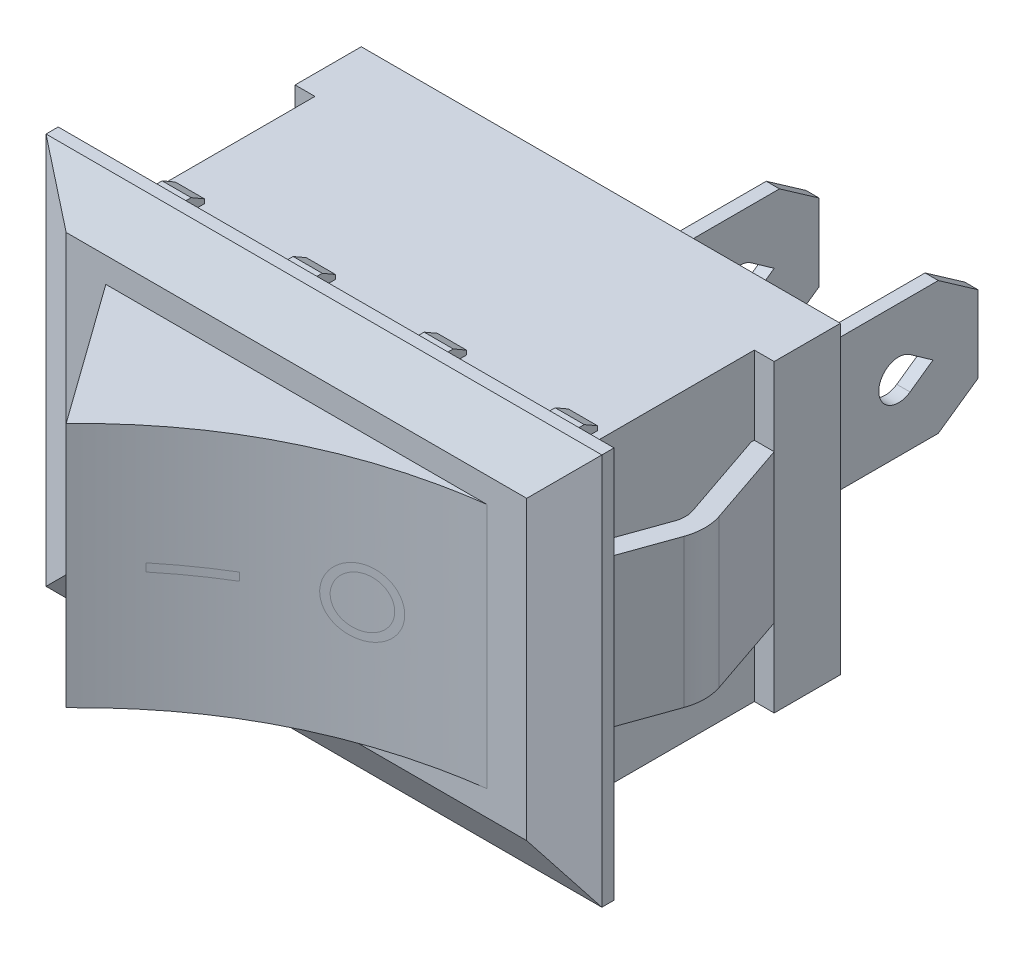
SolidWorks part; units mm, degrees
ref_plane "Front Plane" through (0, 0, 0) normal (0, 0, 1) x (1, 0, 0)
ref_plane "Top Plane" through (0, 0, 0) normal (0, 1, 0) x (1, 0, 0)
ref_plane "Right Plane" through (0, 0, 0) normal (1, 0, 0) x (0, 0, -1)
sketch "Sketch1" plane through (0, 0, 0) normal (0, 0, 1) x (1, 0, 0)
  line L1 (-8.3, -5.75) -> (8.3, -5.75)
  line L2 (-8.3, -5.75) -> (-8.3, 5.75)
  line L3 (-8.3, 5.75) -> (8.3, 5.75)
  line L4 (8.3, -5.75) -> (8.3, 5.75)
  line L5 (-8.3, -5.75) -> (8.3, 5.75) construction
  line L6 (-8.3, 5.75) -> (8.3, -5.75) construction
  point P0 (0, 0)
  dimension "D1" = 16.6
  dimension "D2" = 11.5
extrude "Boss-Extrude1" add sketch "Sketch1" along normal blind 10
sketch "Sketch2" plane through (0, 0, 10) normal (0, 0, 1) x (1, 0, 0)
  line L1 (-10.5, -7.4) -> (10.5, -7.4)
  line L2 (-10.5, -7.4) -> (-10.5, 7.4)
  line L3 (-10.5, 7.4) -> (10.5, 7.4)
  line L4 (10.5, -7.4) -> (10.5, 7.4)
  line L5 (-10.5, -7.4) -> (10.5, 7.4) construction
  line L6 (-10.5, 7.4) -> (10.5, -7.4) construction
  point P0 (0, 0)
  dimension "D1" = 14.8
  dimension "D2" = 21
extrude "Boss-Extrude2" add sketch "Sketch2" along normal blind 1.5
sketch "Sketch3" plane through (0, 0, 0) normal (0, 0, -1) x (-1, 0, 0)
  line L1 (-6.25, -2.5) -> (-5.75, -2.5)
  line L2 (-6.25, -2.5) -> (-6.25, 2.5)
  line L3 (-6.25, 2.5) -> (-5.75, 2.5)
  line L4 (-5.75, -2.5) -> (-5.75, 2.5)
  line L5 (-6.25, -2.5) -> (-5.75, 2.5) construction
  line L6 (-6.25, 2.5) -> (-5.75, -2.5) construction
  line L7 (-0.25, -2.5) -> (0.25, -2.5)
  line L8 (-0.25, -2.5) -> (-0.25, 2.5)
  line L9 (-0.25, 2.5) -> (0.25, 2.5)
  line L10 (0.25, -2.5) -> (0.25, 2.5)
  line L11 (-0.25, -2.5) -> (0.25, 2.5) construction
  line L12 (-0.25, 2.5) -> (0.25, -2.5) construction
  point P0 (-6, 0)
  point P5 (0, 0)
  dimension "D1" = 0.5
  dimension "D2" = 5
  dimension "D3" = 5
  dimension "D4" = 6
  dimension "D5" = 0.5
extrude "Boss-Extrude3" add sketch "Sketch3" along normal blind 8
sketch "Sketch4" plane through (6.25, 0, 0) normal (1, 0, 0) x (0, 0, -1)
  line L0 (2, 2.5) -> (2, 2.1)
  line L1 (8, 2.5) -> (0, 2.5) construction
  line L2 (2, 2.1) -> (2.5, 2.1)
  line L3 (2.5, 2.1) -> (2.5, 2.5)
  line L4 (0, 0) -> (8, 0) construction
  line L5 (8, 2.5) -> (8, -2.5) construction
  line L6 (0, 0.75) -> (0, -0.75)
  line L7 (2, 2.5) -> (2.5, 2.5)
  line L8 (6.5, 2.5) -> (8, 1.4497)
  line L9 (6.5, 2.5) -> (8, 2.5)
  line L10 (8, 2.5) -> (8, 1.4497)
  line L11 (5.4327, 0.6126) -> (6.3, 0)
  line L12 (5.4327, -0.6126) -> (6.3, 0)
  line L13 (8, -2.5) -> (8, -1.4497)
  line L14 (6.5, -2.5) -> (8, -2.5)
  line L15 (6.5, -2.5) -> (8, -1.4497)
  line L16 (2, -2.1) -> (2.5, -2.1)
  line L17 (2, -2.5) -> (2, -2.1)
  line L18 (2, -2.5) -> (2.5, -2.5)
  line L19 (2.5, -2.1) -> (2.5, -2.5)
  arc A0 (0, -0.75) -> (0, 0.75) centre (0, 0) ccw
  arc A1 (5.4327, 0.6126) -> (5.4327, -0.6126) centre (5, 0) ccw
  dimension "D1" = 1.5
  dimension "D7" = 1.5
  dimension "D2" = 0.5
  dimension "D3" = 0.4
  dimension "D4" = 2
  dimension "D5" = 35
  dimension "D6" = 1.5
  dimension "D8" = 5
  dimension "D9" = 1.3
extrude "Cut-Extrude1" cut sketch "Sketch4" against normal through all
sketch "Sketch5" plane through (0, 0, 0) normal (0, 1, 0) x (1, 0, 0)
  line L0 (-8.3, 0) -> (-9.05, 0)
  line L1 (-9.05, 0) -> (-9.05, -2.5)
  line L2 (-9.05, -2.5) -> (-8.3, -2.5)
  line L3 (-8.3, -10) -> (-8.3, 0) construction
  line L4 (-8.3, -2.5) -> (-8.3, 0)
  dimension "D1" = 2.5
  dimension "D2" = 0.75
extrude "Boss-Extrude4" add sketch "Sketch5" along normal up to surface and the other way up to surface
mirror "Mirror1" about plane through (0, 0, 0) normal (1, 0, 0) of "Boss-Extrude4"
sketch "Sketch6" plane through (0, 0, 0) normal (0, 1, 0) x (1, 0, 0)
  line L0 (-9.05, -2.5) -> (-10.1249, -5.6533)
  line L1 (-10.1156, -6.9707) -> (-9.0566, -9.9386)
  line L2 (0, -11.5) -> (0, 0) construction
  line L3 (10.5, -11.5) -> (-10.5, -11.5) construction
  line L4 (-8.3401, -2.742) -> (-9.4432, -5.9779)
  line L5 (-9.4385, -6.6366) -> (-8.3502, -9.6866)
  line L7 (-8.3, -10) -> (-8.3, -2.5) construction
  line L8 (-8.3401, -2.742) -> (-8.3, -2.6243)
  line L9 (-8.3, -2.6243) -> (-8.3, -2.5)
  line L10 (-8.3, -2.5) -> (-9.05, -2.5)
  line L11 (-9.0566, -9.9386) -> (-9.0347, -10)
  line L12 (10.5, -10) -> (-10.5, -10) construction
  line L13 (-9.0347, -10) -> (-8.3, -10)
  line L14 (-8.3, -10) -> (-8.3, -9.8274)
  line L15 (-8.3, -9.8274) -> (-8.3502, -9.6866)
  line L16 (8.3, -9.8274) -> (8.3502, -9.6866)
  line L17 (8.3, -10) -> (8.3, -9.8274)
  line L18 (9.0347, -10) -> (8.3, -10)
  line L19 (9.0566, -9.9386) -> (9.0347, -10)
  line L20 (8.3, -2.5) -> (9.05, -2.5)
  line L21 (8.3, -2.6243) -> (8.3, -2.5)
  line L22 (8.3401, -2.742) -> (8.3, -2.6243)
  line L23 (9.4385, -6.6366) -> (8.3502, -9.6866)
  line L24 (8.3401, -2.742) -> (9.4432, -5.9779)
  line L25 (10.1156, -6.9707) -> (9.0566, -9.9386)
  line L26 (9.05, -2.5) -> (10.1249, -5.6533)
  line L27 (-10.35, -6.3137) -> (-9.0566, -9.9386) construction
  line L28 (-9.05, -2.5) -> (-10.35, -6.3137) construction
  line L29 (-9.5557, -6.308) -> (-8.3502, -9.6866) construction
  line L30 (-8.3401, -2.742) -> (-9.5557, -6.308) construction
  arc A0 (-10.1156, -6.9707) -> (-10.1249, -5.6533) centre (-8.2319, -6.2986) cw
  arc A1 (-9.4385, -6.6366) -> (-9.4432, -5.9779) centre (-8.4966, -6.3005) cw
  arc A2 (9.4385, -6.6366) -> (9.4432, -5.9779) centre (8.4966, -6.3005) ccw
  arc A3 (10.1156, -6.9707) -> (10.1249, -5.6533) centre (8.2319, -6.2986) ccw
  point P37 (-10.35, -6.3137)
  point P41 (-9.5557, -6.308)
  point P44 (9.5557, -6.308)
  point P47 (10.35, -6.3137)
  dimension "D3" = 2
  dimension "D4" = 1
  dimension "D5" = 1
  dimension "D6" = 2
  dimension "D1" = 10.35
  dimension "D2" = 0.75
extrude "Boss-Extrude5" add sketch "Sketch6" along normal blind 2.8 and the other way blind 2.8
chamfer "Chamfer1" distance 1.8 angle 30 4 edges at (-10.5, 0, 11.5) (0, -7.4, 11.5) (10.5, 0, 11.5) (0, 7.4, 11.5)
sketch "Sketch7" plane through (0, 0, 0) normal (0, 1, 0) x (1, 0, 0)
  line L0 (-7.2, -11.5) -> (-3.3987, -16.8)
  line L1 (-8.7, -11.5) -> (8.7, -11.5) construction
  line L2 (-9.05, 0) -> (9.05, 0) construction
  line L3 (-7.2, -11.5) -> (7.2, -11.5)
  spline S0 degree 2 poles (-3.3987, -16.8) (0.9274, -12.3348) (7.2, -11.5) knots 0 0 0 1 1 1
  dimension "D1" = 16.8
  dimension "D2" = 1.5
  dimension "D3" = 1.5
extrude "Boss-Extrude6" add sketch "Sketch7" along normal mid plane 9.3
ref_plane "Plane1" through (6.0406, 0, 12.0798) normal (0.4473, 0, 0.8944) x (0.8944, 0, -0.4473)
sketch "Sketch8" plane through (6.0406, 0, 12.0798) normal (0.4473, 0, 0.8944) x (0.8944, 0, -0.4473)
  line L1 (-8.5, -0.15) -> (-6, -0.15)
  line L2 (-8.5, -0.15) -> (-8.5, 0.15)
  line L3 (-8.5, 0.15) -> (-6, 0.15)
  line L4 (-6, -0.15) -> (-6, 0.15)
  line L5 (-8.5, -0.15) -> (-6, 0.15) construction
  line L6 (-8.5, 0.15) -> (-6, -0.15) construction
  circle A0 centre (-2.5, 0) radius 1.25
  circle A1 centre (-2.5, 0) radius 0.95
  point P0 (-7.25, 0)
  dimension "D4" = 0.3
  dimension "D6" = 2.5
  dimension "D1" = 0.3
  dimension "D2" = 2.5
  dimension "D3" = 6
  dimension "D5" = 2.5
split line "Split Line1"
sketch "Sketch9" plane through (0, 0, 10) normal (0, 0, -1) x (-1, 0, 0)
  line L0 (-9.05, 5.75) -> (9.05, 5.75) construction
  line L1 (-7.975, 5.75) -> (-6.875, 5.75)
  line L2 (-7.975, 5.75) -> (-7.975, 6.2)
  line L3 (-7.975, 6.2) -> (-6.875, 6.2)
  line L4 (-6.875, 5.75) -> (-6.875, 6.2)
  line L5 (-8.3, 5.75) -> (8.3, 5.75) construction
  line L7 (0, 0) -> (0, 6.2) construction
  line L8 (-3.025, 5.75) -> (-1.925, 5.75)
  line L9 (-3.025, 5.75) -> (-3.025, 6.2)
  line L10 (-3.025, 6.2) -> (-1.925, 6.2)
  line L11 (-1.925, 5.75) -> (-1.925, 6.2)
  line L12 (0, 0) -> (-7.7156, 0) construction
  line L13 (1.925, 5.75) -> (1.925, 6.2)
  line L14 (3.025, 6.2) -> (1.925, 6.2)
  line L15 (3.025, 5.75) -> (3.025, 6.2)
  line L16 (3.025, 5.75) -> (1.925, 5.75)
  line L17 (6.875, 5.75) -> (6.875, 6.2)
  line L18 (7.975, 6.2) -> (6.875, 6.2)
  line L19 (7.975, 5.75) -> (7.975, 6.2)
  line L20 (7.975, 5.75) -> (6.875, 5.75)
  line L21 (7.975, -5.75) -> (6.875, -5.75)
  line L22 (7.975, -5.75) -> (7.975, -6.2)
  line L23 (7.975, -6.2) -> (6.875, -6.2)
  line L24 (6.875, -5.75) -> (6.875, -6.2)
  line L25 (3.025, -5.75) -> (1.925, -5.75)
  line L26 (3.025, -5.75) -> (3.025, -6.2)
  line L27 (3.025, -6.2) -> (1.925, -6.2)
  line L28 (1.925, -5.75) -> (1.925, -6.2)
  line L29 (-1.925, -5.75) -> (-1.925, -6.2)
  line L30 (-3.025, -6.2) -> (-1.925, -6.2)
  line L31 (-3.025, -5.75) -> (-3.025, -6.2)
  line L32 (-3.025, -5.75) -> (-1.925, -5.75)
  line L33 (-6.875, -5.75) -> (-6.875, -6.2)
  line L34 (-7.975, -6.2) -> (-6.875, -6.2)
  line L35 (-7.975, -5.75) -> (-7.975, -6.2)
  line L36 (-7.975, -5.75) -> (-6.875, -5.75)
  dimension "D1" = 1.1
  dimension "D2" = 0.45
  dimension "D3" = 1.925
  dimension "D4" = 1.1
  dimension "D5" = 3.85
extrude "Boss-Extrude7" add sketch "Sketch9" along normal blind 1.9
chamfer "Chamfer2" distance 0.5 angle 30 8 edges at (-7.425, -6.2, 8.1) (-2.475, -6.2, 8.1) (2.475, -6.2, 8.1) (7.425, -6.2, 8.1) (-7.425, 6.2, 8.1) (-2.475, 6.2, 8.1) (2.475, 6.2, 8.1) (7.425, 6.2, 8.1)
